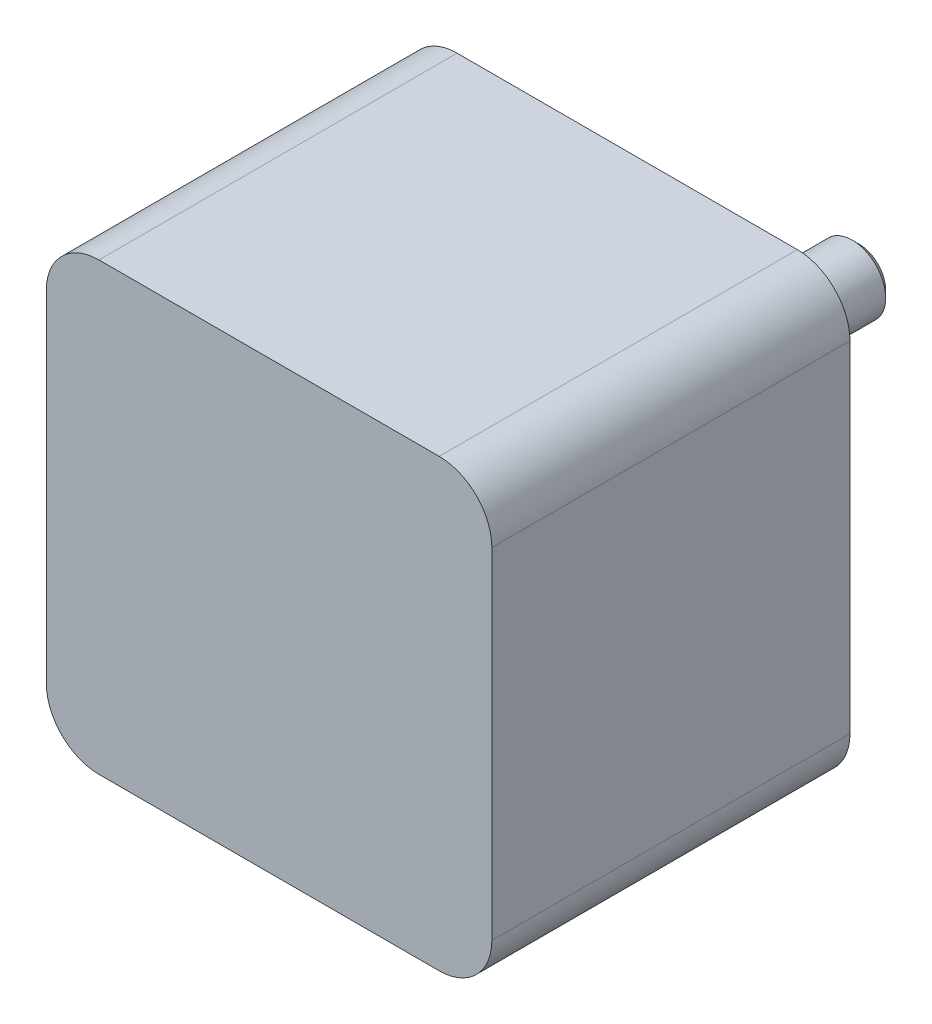
SolidWorks part; units mm, degrees
ref_plane "Front Plane" through (0, 0, 0) normal (0, 0, 1) x (1, 0, 0)
ref_plane "Top Plane" through (0, 0, 0) normal (0, 1, 0) x (1, 0, 0)
ref_plane "Right Plane" through (0, 0, 0) normal (1, 0, 0) x (0, 0, -1)
sketch "Sketch1" plane through (0, 0, 0) normal (0, 0, 1) x (1, 0, 0)
  line L1 (-16.15, -21.15) -> (16.15, -21.15)
  line L2 (-21.15, -16.15) -> (-21.15, 16.15)
  line L3 (-16.15, 21.15) -> (16.15, 21.15)
  line L4 (21.15, -16.15) -> (21.15, 16.15)
  circle A1 centre (15.5, 15.5) radius 1.5875
  circle A2 centre (-15.5, 15.5) radius 1.5875
  circle A3 centre (15.5, -15.5) radius 1.5875
  circle A4 centre (-15.5, -15.5) radius 1.5875
  arc A5 (-16.15, -21.15) -> (-21.15, -16.15) centre (-16.15, -16.15) cw
  arc A6 (16.15, -21.15) -> (21.15, -16.15) centre (16.15, -16.15) ccw
  arc A7 (16.15, 21.15) -> (21.15, 16.15) centre (16.15, 16.15) cw
  arc A8 (-21.15, 16.15) -> (-16.15, 21.15) centre (-16.15, 16.15) cw
  dimension "D1" = 2
  dimension "D3" = 5
  dimension "D2" = 2
extrude "Boss-Extrude1" add sketch "Sketch1" along normal blind 32
sketch "Sketch2" plane through (0, 0, 32) normal (0, 0, 1) x (1, 0, 0)
  line L1 (-16.15, -21.15) -> (16.15, -21.15)
  line L2 (-21.15, -16.15) -> (-21.15, 16.15)
  line L3 (-16.15, 21.15) -> (16.15, 21.15)
  line L4 (21.15, -16.15) -> (21.15, 16.15)
  line L5 (-21.15, -21.15) -> (21.15, 21.15) construction
  line L6 (-21.15, 21.15) -> (21.15, -21.15) construction
  arc A0 (16.15, -21.15) -> (21.15, -16.15) centre (16.15, -16.15) ccw
  arc A1 (-16.15, -21.15) -> (-21.15, -16.15) centre (-16.15, -16.15) cw
  arc A2 (16.15, 21.15) -> (21.15, 16.15) centre (16.15, 16.15) cw
  arc A3 (-21.15, 16.15) -> (-16.15, 21.15) centre (-16.15, 16.15) cw
  point P0 (0, 0)
  dimension "D1" = 5
extrude "Boss-Extrude2" add sketch "Sketch2" along normal blind 2
sketch "Sketch3" plane through (0, 0, 0) normal (0, 0, -1) x (-1, 0, 0)
  circle A0 centre (0, 0) radius 11
extrude "Boss-Extrude3" add sketch "Sketch3" along normal blind 2
sketch "Sketch4" plane through (0, 0, -2) normal (0, 0, -1) x (-1, 0, 0)
  circle A0 centre (0, 0) radius 3.175
extrude "Boss-Extrude4" add sketch "Sketch4" along normal blind 20
chamfer "Chamfer1" distance 0.635 angle 45 1 edges at (-3.175, 0, -22)
